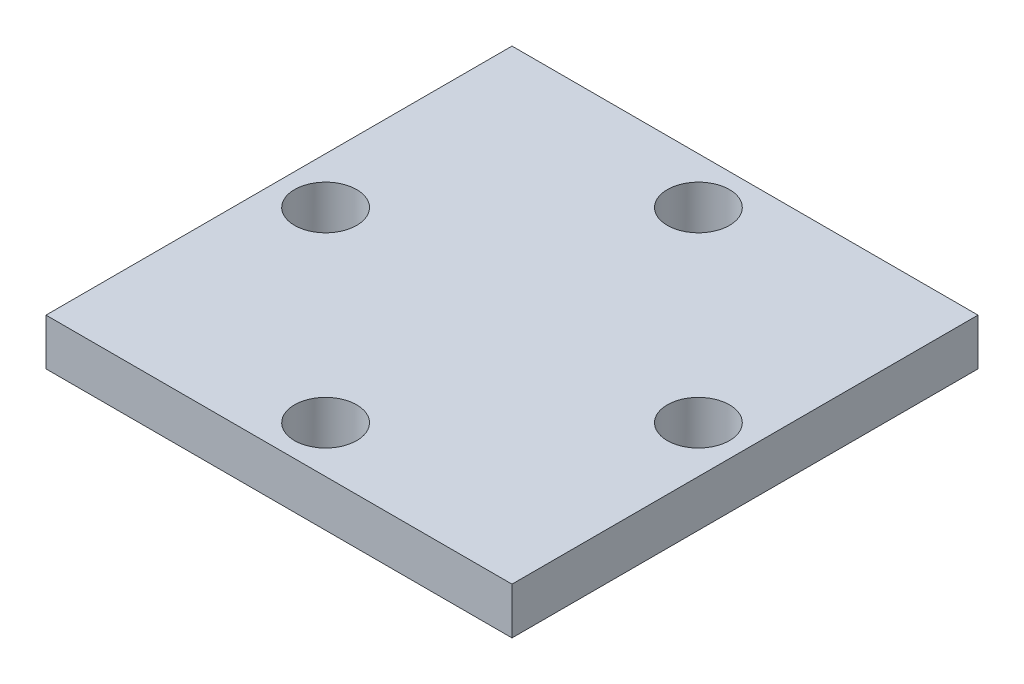
SolidWorks part; units mm, degrees
ref_plane "前基準面" through (0, 0, 0) normal (0, 0, 1) x (1, 0, 0)
ref_plane "上基準面" through (0, 0, 0) normal (0, 1, 0) x (1, 0, 0)
ref_plane "右基準面" through (0, 0, 0) normal (1, 0, 0) x (0, 0, -1)
sketch "草圖1" plane through (0, 0, 0) normal (0, 1, 0) x (1, 0, 0)
  line L1 (15, 15) -> (-15, 15)
  line L2 (15, 15) -> (15, -15)
  line L3 (15, -15) -> (-15, -15)
  line L4 (-15, 15) -> (-15, -15)
  line L5 (15, 15) -> (-15, -15) construction
  line L6 (15, -15) -> (-15, 15) construction
  point P0 (0, 0)
  dimension "D1" = 30
  dimension "D2" = 30
extrude "填料-伸長1" add sketch "草圖1" along normal blind 3
sketch "草圖2" plane through (0, 3, 0) normal (0, 1, 0) x (1, 0, 0)
  line L0 (-16.4553, 0) -> (17.7895, 0) construction
  line L1 (0, 15.7477) -> (0, -16.2329) construction
  line L2 (15, 15) -> (-15, 15) construction
  line L3 (-15, -15) -> (15, -15) construction
  line L6 (-15, 15) -> (-15, -15) construction
  line L7 (15, -15) -> (15, 15) construction
  circle A0 centre (-12, 0) radius 2
  circle A1 centre (12, 0) radius 2
  circle A2 centre (0, 12) radius 2
  circle A3 centre (0, -12) radius 2
  dimension "D1" = 4
  dimension "D2" = 4
  dimension "D3" = 4
  dimension "D4" = 4
  dimension "D5" = 24
  dimension "D6" = 3
  dimension "D7" = 3
  dimension "D9" = 24
  dimension "D10" = 3
extrude "除料-伸長1" cut sketch "草圖2" against normal blind 5
